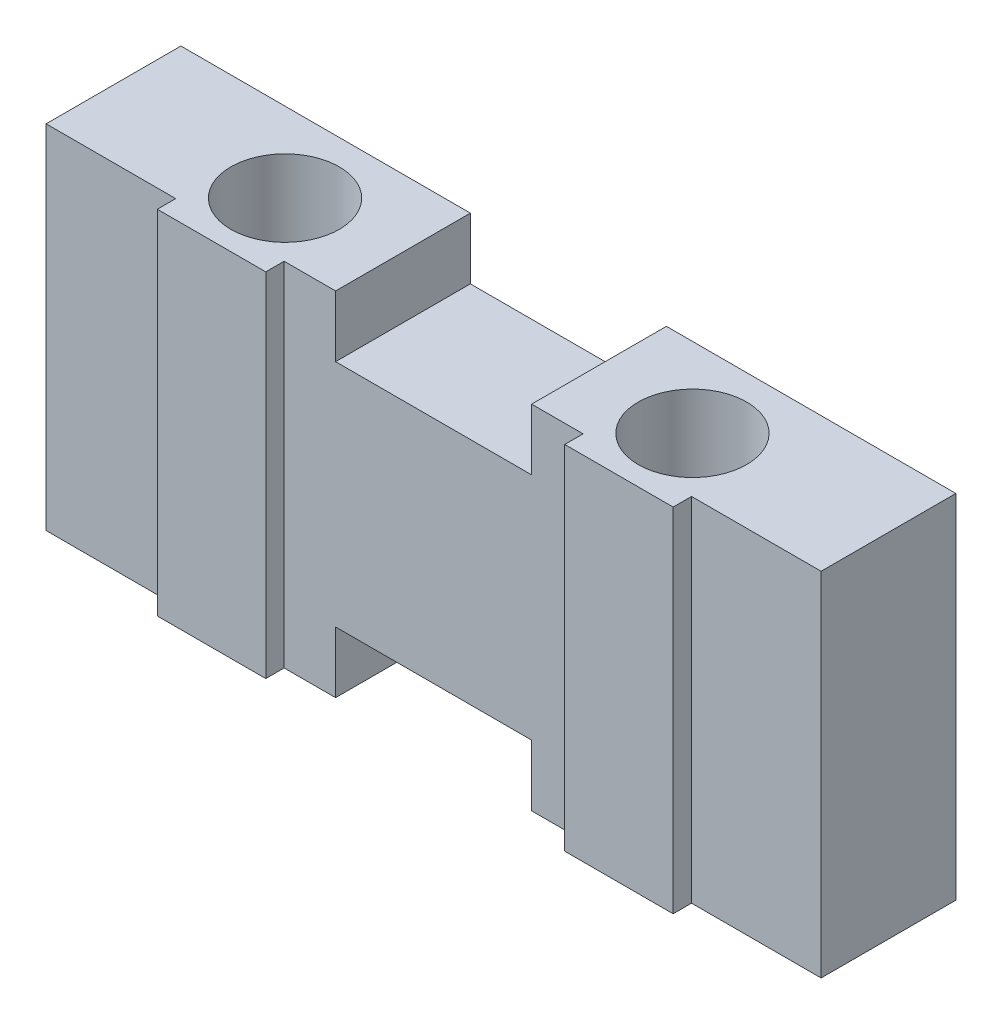
SolidWorks part; units mm, degrees
ref_plane "Front Plane" through (0, 0, 0) normal (0, 0, 1) x (1, 0, 0)
ref_plane "Top Plane" through (0, 0, 0) normal (0, 1, 0) x (1, 0, 0)
ref_plane "Right Plane" through (0, 0, 0) normal (1, 0, 0) x (0, 0, -1)
sketch "Sketch1" plane through (0, 0, 0) normal (0, 0, 1) x (1, 0, 0)
  line L12 (-1.6, 1) -> (1.6, 1)
  line L13 (1.6, 1) -> (1.6, 0)
  line L14 (1.6, 0) -> (6.325, 0)
  line L15 (6.325, 0) -> (6.325, 5.75)
  line L16 (6.325, 5.75) -> (1.6, 5.75)
  line L17 (1.6, 5.75) -> (1.6, 4.75)
  line L18 (1.6, 4.75) -> (-1.6, 4.75)
  line L19 (-1.6, 4.75) -> (-1.6, 5.75)
  line L20 (-1.6, 5.75) -> (-6.325, 5.75)
  line L21 (-6.325, 5.75) -> (-6.325, 0)
  line L22 (-6.325, 0) -> (-1.6, 0)
  line L23 (-1.6, 0) -> (-1.6, 1)
  line L24 (-1.6, 1) -> (1.6, 1)
  line L25 (1.6, 1) -> (1.6, 0)
  line L26 (1.6, 0) -> (6.325, 0)
  line L27 (6.325, 0) -> (6.325, 5.75)
  line L28 (6.325, 5.75) -> (1.6, 5.75)
  line L29 (1.6, 5.75) -> (1.6, 4.75)
  line L30 (1.6, 4.75) -> (-1.6, 4.75)
  line L31 (-1.6, 4.75) -> (-1.6, 5.75)
  line L32 (-1.6, 5.75) -> (-6.325, 5.75)
  line L33 (-6.325, 5.75) -> (-6.325, 0)
  line L34 (-6.325, 0) -> (-1.6, 0)
  line L35 (-1.6, 0) -> (-1.6, 1)
  dimension "D1" = 0
extrude "Extrude1" add sketch "Sketch1" along normal blind 2.5
sketch "Sketch2" plane through (0, 5.75, 0) normal (0, 1, 0) x (-1, 0, 0)
  line L0 (1.6, 2.5) -> (6.325, 2.5) construction
  line L1 (6.325, 2.5) -> (6.325, 0) construction
  line L2 (-6.325, 2.5) -> (-6.325, 0) construction
  line L3 (6.325, 2.2) -> (4.21, 2.2)
  line L4 (4.21, 2.2) -> (4.21, 2.5)
  line L5 (6.325, 2.2) -> (6.325, 2.5)
  line L6 (2.44, 2.5) -> (2.44, 2.2)
  line L7 (2.44, 2.2) -> (-2.44, 2.2)
  line L8 (-2.44, 2.2) -> (-2.44, 2.5)
  line L9 (-6.325, 2.5) -> (-1.6, 2.5) construction
  line L10 (6.325, 2.5) -> (4.21, 2.5)
  line L11 (-4.21, 2.5) -> (-4.21, 2.2)
  line L12 (-4.21, 2.2) -> (-6.325, 2.2)
  line L13 (2.44, 1.3) -> (2.44, 3.9376) construction
  line L14 (4.21, 1.3) -> (4.21, 3.9376) construction
  line L15 (-2.44, 1.3) -> (-2.44, 3.2023) construction
  line L16 (-4.21, 1.3) -> (-4.21, 3.2023) construction
  line L17 (2.44, 2.5) -> (-2.44, 2.5)
  line L18 (-2.44, 2.5) -> (-2.4341, 2.5524)
  line L19 (-6.325, 2.2) -> (-6.325, 2.5)
  line L20 (-6.325, 2.5) -> (-4.21, 2.5)
  circle A0 centre (3.325, 1.3) radius 0.885
  circle A1 centre (-3.325, 1.3) radius 0.885
  line M3 (6.325, 2.5) -> (1.6, 2.5)
  line M4 (1.6, 2.5) -> (1.6, 0)
  dimension "D1" = 1.77
  dimension "D2" = 1.2
  dimension "D3" = 3
  dimension "D4" = 3
  dimension "D5" = 0.3
extrude "Cut-Extrude1" cut sketch "Sketch2" against normal up to next contours A0 | A1 | L17 L8 L7 M4 | L7 L6 M4 M3 | L11 L20 L19 L12 | L10 L4 L3 L5
